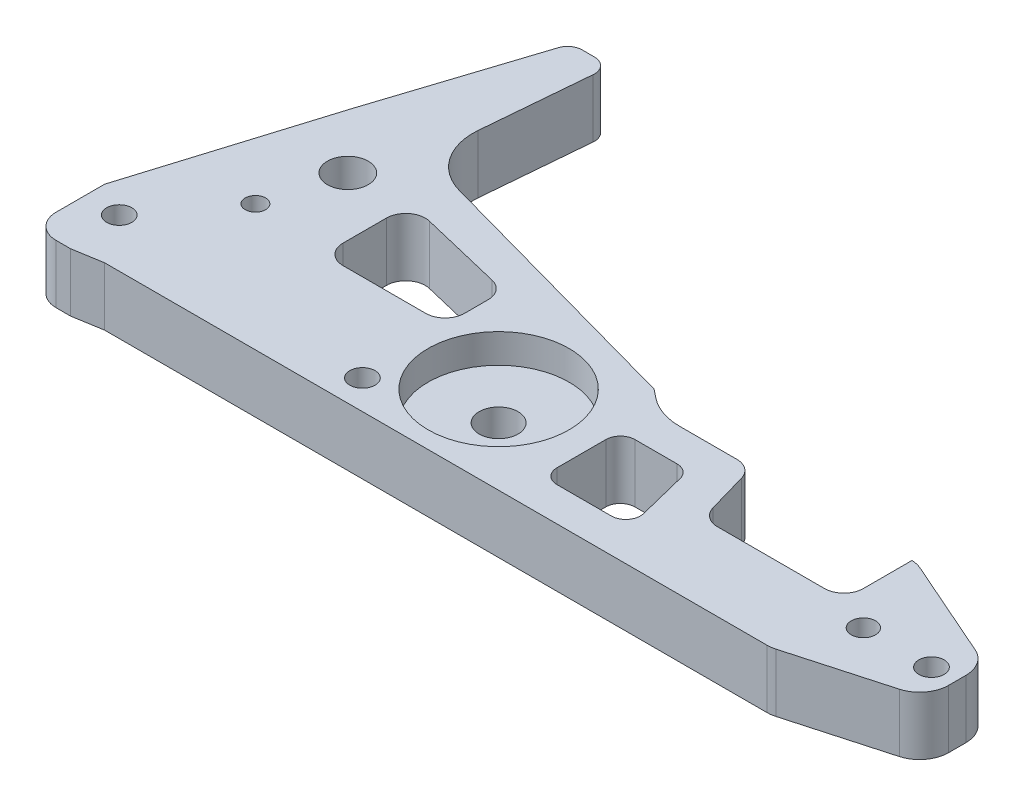
SolidWorks part; units mm, degrees
material "ABS"
ref_plane "Front Plane" through (0, 0, 0) normal (0, 0, 1) x (1, 0, 0)
ref_plane "Top Plane" through (0, 0, 0) normal (0, 1, 0) x (1, 0, 0)
ref_plane "Right Plane" through (0, 0, 0) normal (1, 0, 0) x (0, 0, -1)
sketch "Sketch1" plane through (0, 0, 0) normal (0, 1, 0) x (1, 0, 0)
  line L0 (162, 19) -> (137, 30)
  line L5 (162, 7) -> (137, 0)
  line L7 (-14, 14) -> (-14, 2)
  line L9 (0, 0) -> (137, 0)
  line L10 (162, 7) -> (162, 19)
  line L12 (-14, 14) -> (-2, 53)
  line L13 (83.9687, 30) -> (137, 30)
  line L15 (-2, 53) -> (9, 87)
  line L16 (9, 87) -> (17, 87)
  line L18 (-14, 2) -> (-14, -1)
  line L19 (-14, -1) -> (-6, -1)
  line L22 (-6, -1) -> (0, 0)
  line L23 (13.9687, 52) -> (78.9687, 34)
  line L24 (78.9687, 34) -> (83.9687, 30)
  line L25 (17, 87) -> (13.9687, 52)
  circle A0 centre (-7, 10) radius 2.6
  circle A3 centre (157, 13) radius 2.6
  circle A4 centre (5, 26) radius 2.1
  circle A6 centre (9, 41) radius 4.2
  circle A8 centre (143, 13) radius 2.5
  dimension "D9" = 5.2
  dimension "D12" = 5
  dimension "D15" = 16
  dimension "D13" = 5.2
  dimension "D17" = 4.2
  dimension "D20" = 6
  dimension "D23" = 8.4
  dimension "D27" = 13
  dimension "D3" = 46
  dimension "D4" = 7
  dimension "D5" = 25
  dimension "D6" = 25
  dimension "D7" = 164
  dimension "D8" = 12
  dimension "D10" = 7
  dimension "D11" = 8
  dimension "D14" = 41
  dimension "D16" = 5
  dimension "D18" = 8
  dimension "D19" = 12
  dimension "D21" = 10
  dimension "D22" = 70
  dimension "D24" = 18
  dimension "D25" = 12
  dimension "D26" = 16
  dimension "D28" = 12
  dimension "D29" = 11
  dimension "D30" = 3
  dimension "D31" = 8
  dimension "D32" = 65
  dimension "D34" = 14
  dimension "D38" = 4
  dimension "D39" = 30
  dimension "D40" = 13
extrude "Boss-Extrude1" add sketch "Sketch1" along normal blind 12
fillet "Fillet2" radius 6 4 edges at (137, 6, 0) (162, 6, -7) (162, 6, -19) (137, 6, -30)
fillet "Fillet3" radius 3 2 edges at (9, 6, -87) (17, 6, -87)
sketch "Sketch4" plane through (0, 12, 0) normal (0, 1, 0) x (1, 0, 0)
  line L0 (21, 42) -> (21, 24)
  line L6 (21, 42) -> (46, 36)
  line L7 (46, 36) -> (46, 24)
  line L14 (97, 23.0435) -> (83, 23.0435)
  line L15 (83, 23.0435) -> (83, 7)
  line L17 (83, 7) -> (101, 7)
  line L18 (101, 7) -> (97, 23.0435)
  line L21 (46, 24) -> (21, 24)
  circle A0 centre (9, 41) radius 4.2 construction
  dimension "D1" = 12
  dimension "D2" = 1
  dimension "D3" = 18
  dimension "D4" = 62
  dimension "D5" = 25
  dimension "D7" = 14
  dimension "D8" = 12
  dimension "D10" = 18
extrude "Cut-Extrude1" cut sketch "Sketch4" against normal through all
sketch "Sketch5" plane through (0, 12, 0) normal (0, 1, 0) x (1, 0, 0)
  line L0 (0, 0) -> (136.1758, 0) construction
  circle A0 centre (63, 18) radius 4
  circle A2 centre (-7, 10) radius 2.6 construction
  dimension "D3" = 8
  dimension "D1" = 70
  dimension "D2" = 18
extrude "Cut-Extrude2" cut sketch "Sketch5" against normal through all
sketch "Sketch6" plane through (0, 12, 0) normal (0, 1, 0) x (1, 0, 0)
  circle A0 centre (63, 18) radius 14.5
  dimension "D1" = 29
extrude "Cut-Extrude3" cut sketch "Sketch6" against normal blind 6
fillet "Fillet4" radius 12 2 edges at (83.9687, 6, -30) (13.9687, 6, -52)
sketch "Sketch7" plane through (0, 12, 0) normal (0, 1, 0) x (1, 0, 0)
  circle A0 centre (47, 6) radius 2.6
  circle A1 centre (9, 41) radius 4.2 construction
  dimension "D3" = 5.2
  dimension "D1" = 6
  dimension "D2" = 38
extrude "Cut-Extrude4" cut sketch "Sketch7" against normal through all
fillet "Fillet6" radius 3 4 edges at (101, 6, -7) (97, 6, -23.0435) (83, 6, -7) (83, 6, -23.0435)
fillet "Fillet8" radius 5 1 edges at (-14, 6, 1)
fillet "Fillet9" radius 4 4 edges at (21, 6, -24) (46, 6, -36) (21, 6, -42) (46, 6, -24)
sketch "Sketch10" plane through (0, 12, 0) normal (0, 1, 0) x (1, 0, 0)
  line L0 (103, 30) -> (107, 16)
  line L1 (135.7384, 30) -> (88.1781, 30) construction
  line L2 (107, 16) -> (136, 16)
  line L3 (136, 16) -> (136, 30)
  line L4 (136, 30) -> (103, 30)
  line L5 (83, 20.0435) -> (83, 10) construction
  dimension "D1" = 14
  dimension "D2" = 24
  dimension "D3" = 20
  dimension "D4" = 33
extrude "Cut-Extrude6" cut sketch "Sketch10" against normal through all
fillet "Fillet10" radius 4 3 edges at (136, 6, -16) (107, 6, -16) (103, 6, -30)
